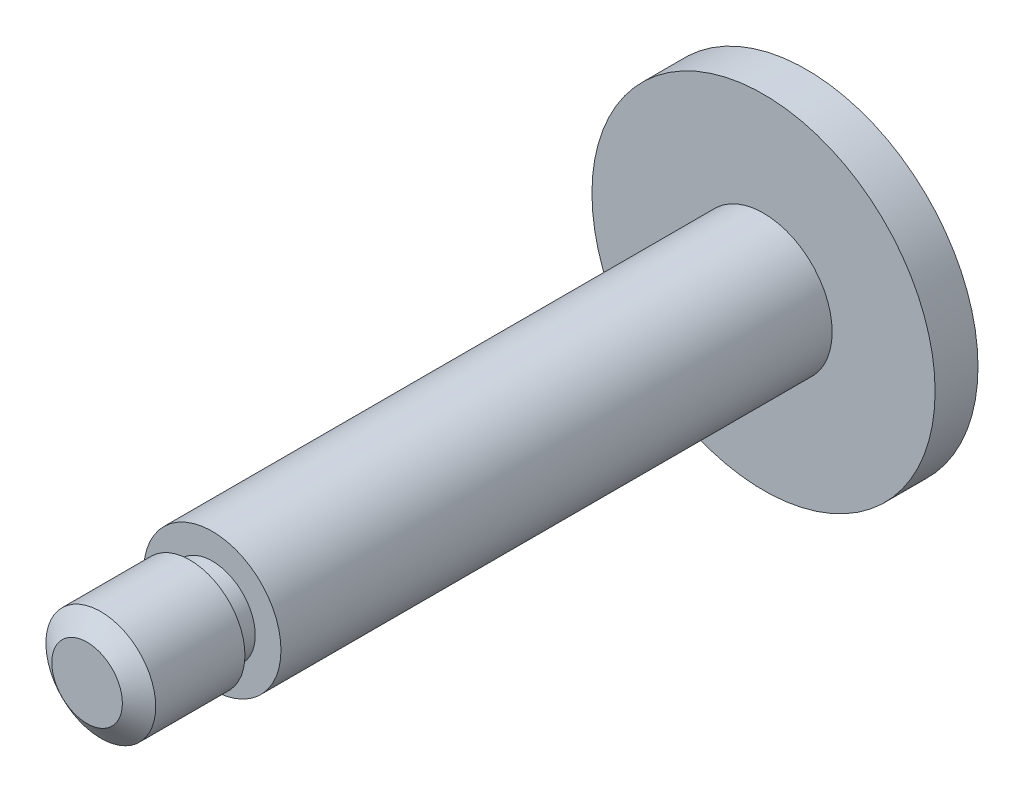
SolidWorks part; units mm, degrees
other "Objet de détail4"
other "Objet de détail11"
other "Objet de détail9"
ref_plane "Plan de face" through (0, 0, 0) normal (0, 0, 1) x (1, 0, 0)
ref_plane "Plan de dessus" through (0, 0, 0) normal (0, 1, 0) x (1, 0, 0)
ref_plane "Plan de droite" through (0, 0, 0) normal (1, 0, 0) x (0, 0, -1)
sketch "Esquisse1" plane through (0, 0, 0) normal (0, 0, 1) x (1, 0, 0)
  circle A0 centre (0, 0) radius 20
extrude "Boss.-Extru.1" add sketch "Esquisse1" along normal blind 5
sketch "Esquisse2" plane through (0, 0, 5) normal (0, 0, 1) x (1, 0, 0)
  circle A0 centre (0, 0) radius 8
extrude "Boss.-Extru.2" add sketch "Esquisse2" along normal blind 64.25
sketch "Esquisse3" plane through (0, 0, 69.25) normal (0, 0, 1) x (1, 0, 0)
  circle A0 centre (0, 0) radius 5
extrude "Boss.-Extru.3" add sketch "Esquisse3" along normal blind 2.6
sketch "Esquisse4" plane through (0, 0, 71.85) normal (0, 0, 1) x (1, 0, 0)
  circle A0 centre (0, 0) radius 6.4
extrude "Boss.-Extru.4" add sketch "Esquisse4" along normal blind 12
chamfer "Chanfrein1" distance 1.6 angle 55 1 edges at (6.4, 0, 83.85)
